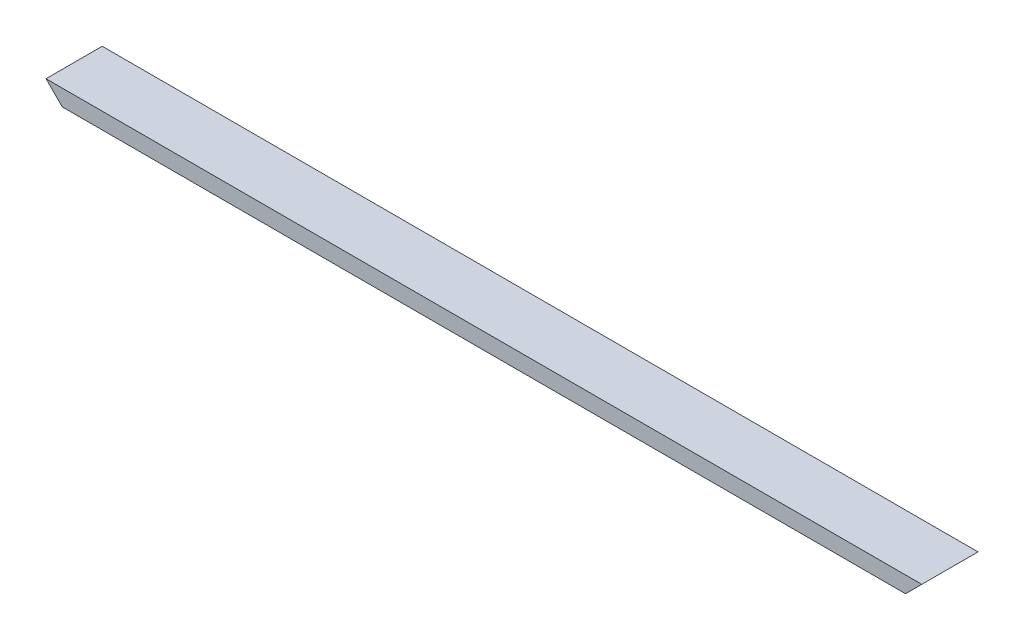
SolidWorks part; units mm, degrees
material "Stainless Steel (ferritic)"
ref_plane "Front Plane" through (0, 0, 0) normal (0, 0, 1) x (1, 0, 0)
ref_plane "Top Plane" through (0, 0, 0) normal (0, 1, 0) x (1, 0, 0)
ref_plane "Right Plane" through (0, 0, 0) normal (1, 0, 0) x (0, 0, -1)
sketch "Sketch1" plane through (0, 0, 0) normal (1, 0, 0) x (0, 0, -1)
  line L0 (-17.5, 4) -> (17.5, 4)
  line L1 (-19, -5.5) -> (19, -5.5)
  line L2 (-19, -5.5) -> (-19, 5.5)
  line L3 (-19, 5.5) -> (19, 5.5)
  line L4 (19, -5.5) -> (19, 5.5)
  line L5 (-19, -5.5) -> (19, 5.5) construction
  line L6 (-19, 5.5) -> (19, -5.5) construction
  line L7 (17.5, -4) -> (17.5, 4)
  line L8 (-17.5, -4) -> (17.5, -4)
  line L9 (-17.5, -4) -> (-17.5, 4)
  point P0 (0, 0)
  dimension "D1" = 38
  dimension "D2" = 11
  dimension "D3" = 1.5
extrude "Boss-Extrude1" add sketch "Sketch1" along normal blind 592
sketch "Sketch2" plane through (0, 0, -19) normal (0, 0, -1) x (-1, 0, 0)
  line L0 (0, 5.5) -> (-11, -5.5)
  line L1 (-592, -5.5) -> (0, -5.5) construction
  line L2 (0, -5.5) -> (0, 5.5) construction
  dimension "D1" = 45
extrude "Cut-Extrude1" cut sketch "Sketch2" against normal through all and the other way through all
sketch "Sketch3" plane through (0, 0, -19) normal (0, 0, -1) x (-1, 0, 0)
  line L0 (-592, 5.5) -> (-581, -5.5)
  line L1 (-592, -5.5) -> (-11, -5.5) construction
  line L2 (-592, -5.5) -> (-592, 5.5) construction
  dimension "D1" = 45
extrude "Cut-Extrude3" cut sketch "Sketch3" against normal through all and the other way through all flip side to cut
